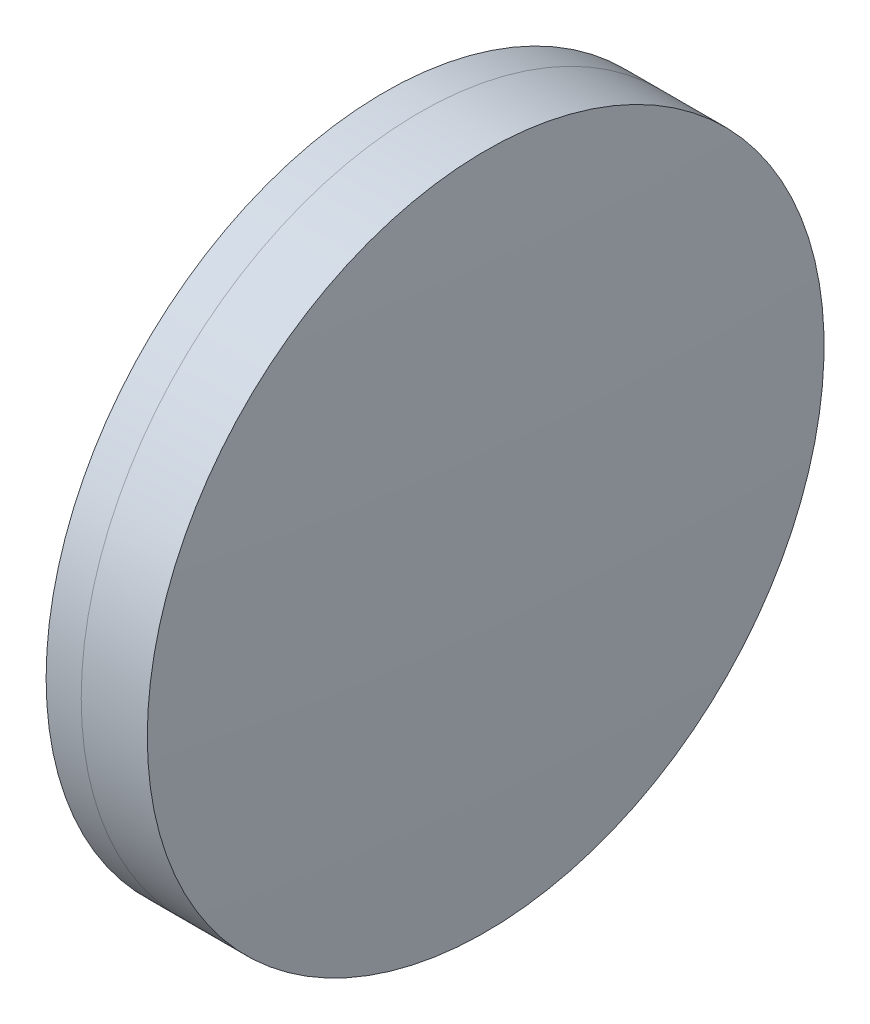
SolidWorks part; units mm, degrees
ref_plane "前视基准面" through (0, 0, 0) normal (0, 0, 1) x (1, 0, 0)
ref_plane "上视基准面" through (0, 0, 0) normal (0, 1, 0) x (1, 0, 0)
ref_plane "右视基准面" through (0, 0, 0) normal (1, 0, 0) x (0, 0, -1)
sketch "草图1" plane through (0, 0, 0) normal (0, 1, 0) x (1, 0, 0)
  line L0 (-9.7026, 0) -> (80.552, 0) construction
  line L1 (77.5145, -12.5) -> (78.8111, -12.5)
  line L2 (77.5145, 12.5) -> (78.8111, 12.5)
  arc A0 (78.8111, -12.5) -> (78.8111, 12.5) centre (14.8797, 0) ccw
  arc A1 (77.5145, 12.5) -> (77.5145, -12.5) centre (175.6587, 0) ccw
  point P10 (76.7217, 0)
  point P11 (80.0217, 0)
  dimension "D3" = 98.937
  dimension "D4" = 65.142
  dimension "D1" = 12.5
  dimension "D2" = 12.5
  dimension "D5" = 3.3
revolve "旋转1" add sketch "草图1" angle 360 about L0
sketch "草图2" plane through (0, 0, 0) normal (0, 1, 0) x (1, 0, 0)
  line L0 (-0.5519, 0) -> (92.6188, 0) construction
  line L2 (78.8111, 12.5) -> (81.2518, 12.5)
  line L3 (78.8111, -12.5) -> (81.2518, -12.5)
  arc A0 (81.2518, -12.5) -> (81.2518, 12.5) centre (-129.8123, 0) ccw
  arc A1 (78.8111, -12.5) -> (78.8111, 12.5) centre (14.8797, 0) ccw construction
  arc A2 (78.8111, -12.5) -> (78.8111, 12.5) centre (14.8797, 0) ccw
  point P4 (80.0217, 0)
  point P8 (81.6217, 0)
  point P9 (92.6188, 0)
  dimension "D1" = 211.434
  dimension "D2" = 1.6
revolve "旋转3" add sketch "草图2" angle 360 about L0
